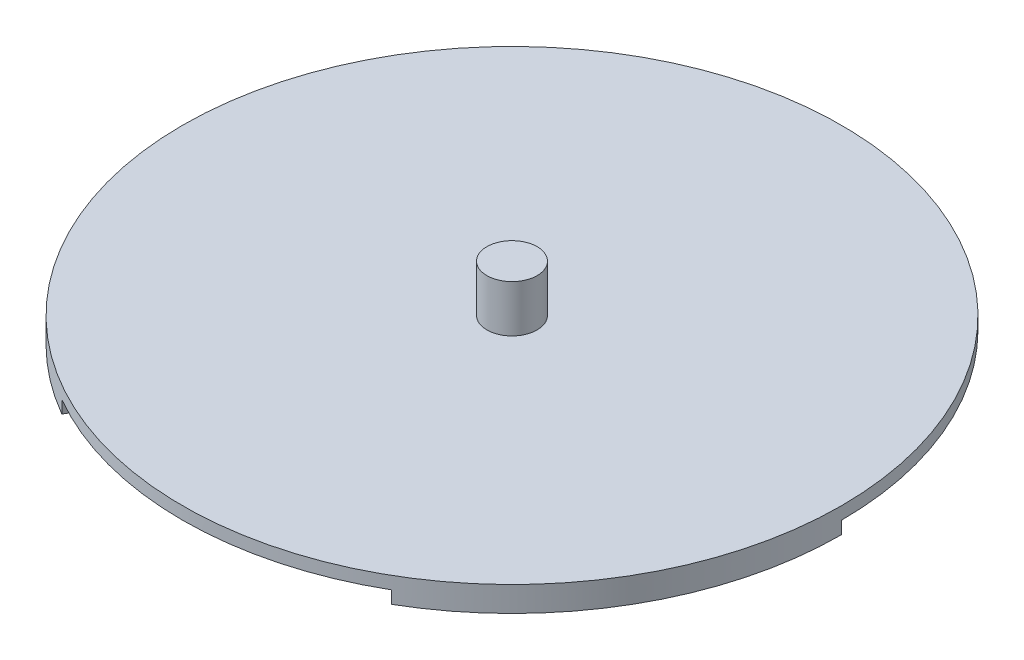
SolidWorks part; units mm, degrees
ref_plane "Front Plane" through (0, 0, 0) normal (0, 0, 1) x (1, 0, 0)
ref_plane "Top Plane" through (0, 0, 0) normal (0, 1, 0) x (1, 0, 0)
ref_plane "Right Plane" through (0, 0, 0) normal (1, 0, 0) x (0, 0, -1)
sketch "Sketch1" plane through (0, 0, 0) normal (0, 0, 1) x (1, 0, 0)
  line L0 (105, 8) -> (0, 8)
  line L1 (0, 8) -> (0, 0)
  line L2 (0, 0) -> (105, 0)
  line L3 (105, 0) -> (105, 8)
  line L4 (0, 8) -> (0, 0) construction
  point P4 (0, 0)
  dimension "D1" = 105
  dimension "D2" = 8
revolve "Revolve1" add sketch "Sketch1" angle 360 about L4
sketch "Sketch6" plane through (0, 0, 0) normal (0, -1, 0) x (1, 0, 0)
  line L7 (92.5, 0) -> (46.25, 80.1073)
  line L8 (46.25, 80.1073) -> (-46.25, 80.1073)
  line L9 (-46.25, 80.1073) -> (-92.5, 0)
  line L10 (-92.5, 0) -> (-46.25, -80.1073)
  line L11 (-46.25, -80.1073) -> (46.25, -80.1073)
  line L12 (46.25, -80.1073) -> (92.5, 0)
  circle A0 centre (0, 0) radius 92.5 construction
  dimension "D1" = 185
sketch "Sketch2" plane through (0, 0, 0) normal (0, -1, 0) x (1, 0, 0)
  line L0 (46.25, 80.1073) -> (52.5, 90.9327)
  line L1 (105, 0) -> (92.5, 0)
  arc A0 (52.5, 90.9327) -> (105, 0) centre (0, 0) ccw
  arc A1 (92.5, 0) -> (46.25, 80.1073) centre (0, 0) ccw
  circle A4 centre (0, 0) radius 92.5 construction
  circle A5 centre (0, 0) radius 105 construction
  point P7 (0, 0)
  point P9 (0, 0)
  point P11 (0, 0)
  point P15 (104.6073, 9.0724)
  point P16 (0, 0)
  dimension "D1" = 12.5
extrude "Cut-Extrude1" cut sketch "Sketch2" against normal blind 4
sketch "Sketch3" plane through (0, 4, 0) normal (0, -1, 0) x (1, 0, 0)
  line L0 (-92.5, 0) -> (-105, 0)
  line L1 (-52.5, 90.9327) -> (-46.25, 80.1073)
  line L3 (46.25, 80.1073) -> (52.5, 90.9327) construction
  arc A0 (-105, 0) -> (-52.5, 90.9327) centre (0, 0) cw
  arc A1 (-46.25, 80.1073) -> (-92.5, 0) centre (0, 0) ccw
  circle A2 centre (0, 0) radius 105 construction
  circle A3 centre (0, 0) radius 92.5 construction
  point P5 (0, 0)
  point P7 (0, 0)
  point P12 (-46.25, 80.1073)
  point P13 (-57.3241, 87.9713)
  point P14 (-105, 0)
  point P15 (-54.919, 89.4925)
  point P16 (-104.9927, -1.2383)
  point P18 (0, 0)
  point P19 (-41.16, 96.5964)
  point P21 (-104.9766, 2.2175)
  point P22 (-104.9756, -2.2629)
extrude "Boss-Extrude1" add sketch "Sketch3" along normal blind 4
sketch "Sketch4" plane through (0, 4, 0) normal (0, -1, 0) x (1, 0, 0)
  line L0 (-52.5, -90.9327) -> (-46.25, -80.1073)
  line L1 (46.25, -80.1073) -> (52.5, -90.9327)
  line L2 (-105, 0) -> (-92.5, 0) construction
  arc A0 (52.5, -90.9327) -> (-52.5, -90.9327) centre (0, 0) cw
  arc A1 (-46.25, -80.1073) -> (46.25, -80.1073) centre (0, 0) ccw
  circle A2 centre (0, 0) radius 105 construction
  arc A3 (-46.25, 80.1073) -> (-92.5, 0) centre (0, 0) ccw construction
  point P5 (0, 0)
  point P15 (0, 0)
  point P16 (0, 0)
  point P18 (0, 0)
extrude "Boss-Extrude2" add sketch "Sketch4" along normal blind 4
sketch "Sketch5" plane through (0, 0, 0) normal (0, 0, 1) x (1, 0, 0)
  line L0 (8, 23) -> (0, 23)
  line L1 (0, 23) -> (0, 8)
  line L2 (0, 8) -> (8, 8)
  line L3 (8, 8) -> (8, 23)
  line L4 (0, 23) -> (0, 8) construction
  line L5 (105, 8) -> (-105, 8) construction
  point P4 (0, 0)
  dimension "D1" = 8
  dimension "D2" = 15
revolve "Revolve2" add sketch "Sketch5" angle 360 about L4
